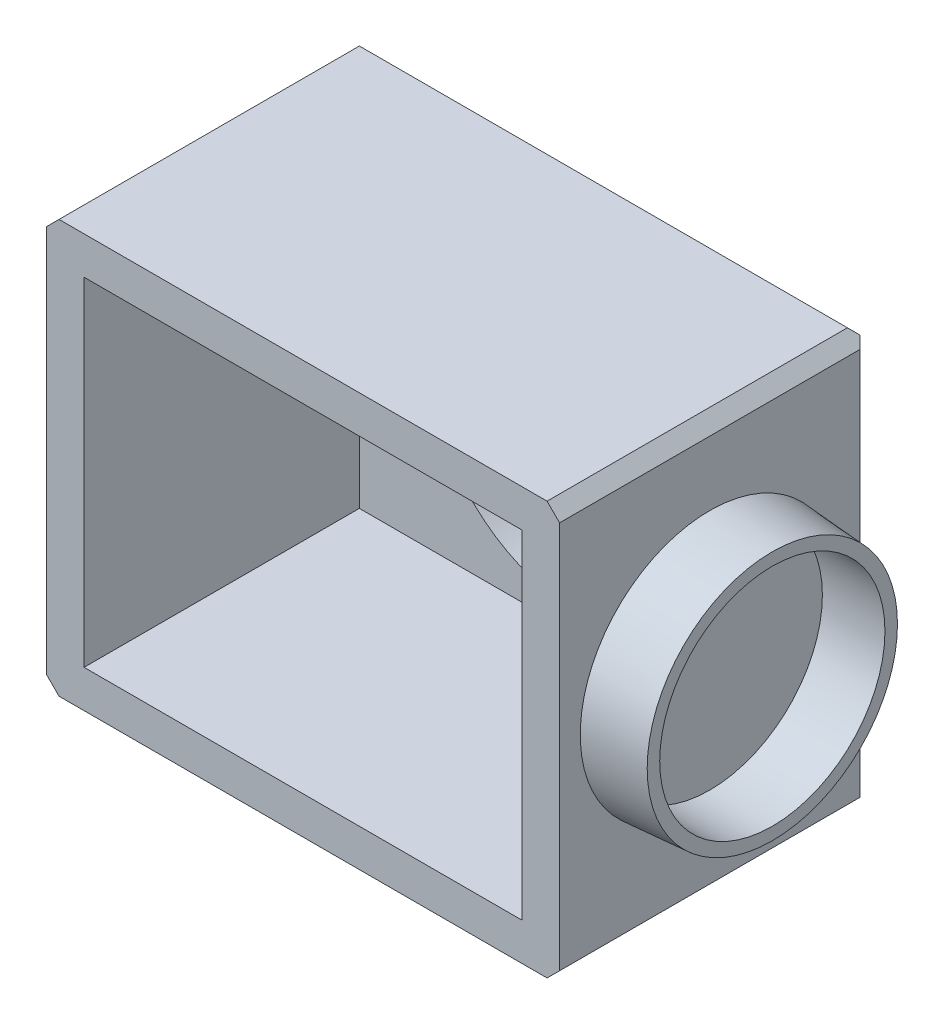
SolidWorks part; units mm, degrees
ref_plane "Спереди" through (0, 0, 0) normal (0, 0, 1) x (1, 0, 0)
ref_plane "Сверху" through (0, 0, 0) normal (0, 1, 0) x (1, 0, 0)
ref_plane "Справа" through (0, 0, 0) normal (1, 0, 0) x (0, 0, -1)
sketch "Эскиз1" plane through (0, 0, 0) normal (0, 0, 1) x (1, 0, 0)
  line L0 (0, 27.9582) -> (0, -29.9104) construction
  line L1 (-31.3048, 0) -> (38.6952, 0) construction
  line L3 (-17.5, 13.5) -> (17.5, 13.5)
  line L4 (-17.5, 13.5) -> (-17.5, -13.5)
  line L5 (-17.5, -13.5) -> (17.5, -13.5)
  line L6 (17.5, 13.5) -> (17.5, -13.5)
  point P9 (0, 13.5)
  point P10 (17.5, 0)
  dimension "D1" = 35
  dimension "D2" = 27
extrude "Вытянуть-Тонкостенный1" add sketch "Эскиз1" along normal blind 22 thin contours L4 L5 L6 L3 thin type one direction wall 3
sketch "Эскиз6" plane through (0, 0, 0) normal (0, 0, -1) x (-1, 0, 0)
  line L1 (-20.5, 16.5) -> (20.5, 16.5)
  line L2 (-20.5, 16.5) -> (-20.5, -16.5)
  line L3 (-20.5, -16.5) -> (20.5, -16.5)
  line L4 (20.5, 16.5) -> (20.5, -16.5)
extrude "Бобышка-Вытянуть1" add sketch "Эскиз6" along normal blind 3
sketch "Эскиз7" plane through (0, 0, -3) normal (0, 0, -1) x (-1, 0, 0)
  circle A0 centre (0, 0) radius 12
  dimension "D1" = 24
extrude "Вырез-Вытянуть1" cut sketch "Эскиз7" against normal blind 5
chamfer "Фаска1" distance 1 angle 45 1 edges at (0, 16.5, -3)
chamfer "Фаска2" distance 1 angle 45 1 edges at (20.5, -0.5, -3)
chamfer "Фаска3" distance 1 angle 45 1 edges at (-20.5, -0.5, -3)
chamfer "Фаска4" distance 1 angle 45 1 edges at (0, -16.5, -3)
sketch "Эскиз8" plane through (0, 0, 0) normal (0, 0, 1) x (1, 0, 0)
  line L0 (0, 17.3986) -> (0, -17.6203) construction
  line L1 (-23.4193, 0) -> (22.042, 0) construction
  circle A0 centre (14.5, 0) radius 1.1
  circle A1 centre (-14.5, 0) radius 1.1
  dimension "D2" = 2.2
  dimension "D1" = 14.5
extrude "Бобышка-Вытянуть3" add sketch "Эскиз8" along normal blind 6 draft 3
chamfer "Фаска5" distance 1 angle 45 1 edges at (-20.5, 16.5, 10)
chamfer "Фаска6" distance 1 angle 45 1 edges at (20.5, 16.5, 10)
chamfer "Фаска7" distance 1 angle 45 1 edges at (20.5, -16.5, 10)
chamfer "Фаска8" distance 1 angle 45 1 edges at (-20.5, -16.5, 10)
sketch "Эскиз9" plane through (20.5, 0, 0) normal (1, 0, 0) x (0, 0, -1)
  line L0 (-10, 15.5) -> (-10, -16.5) construction
  line L1 (2, 15.5) -> (-22, 15.5) construction
  line L2 (2, -16.5) -> (-22, -16.5) construction
  line L3 (-23.6982, 0) -> (3.6982, 0) construction
  circle A0 centre (-10, 0) radius 10.35
  point P9 (-10, 0)
  dimension "D1" = 20.7
extrude "Бобышка-Вытянуть4" add sketch "Эскиз9" along normal blind 5 draft 4
sketch "Эскиз10" plane through (25.5, 0, 0) normal (1, 0, 0) x (0, 0, -1)
  line L0 (-20.0004, 0) -> (0.0004, 0) construction
  line L1 (-10, -10.0004) -> (-10, 10.0004) construction
  circle A0 centre (-10, 0) radius 10.0004 construction
  circle A1 centre (-10, 0) radius 9
  dimension "D1" = 18
extrude "Вырез-Вытянуть2" cut sketch "Эскиз10" against normal blind 5
